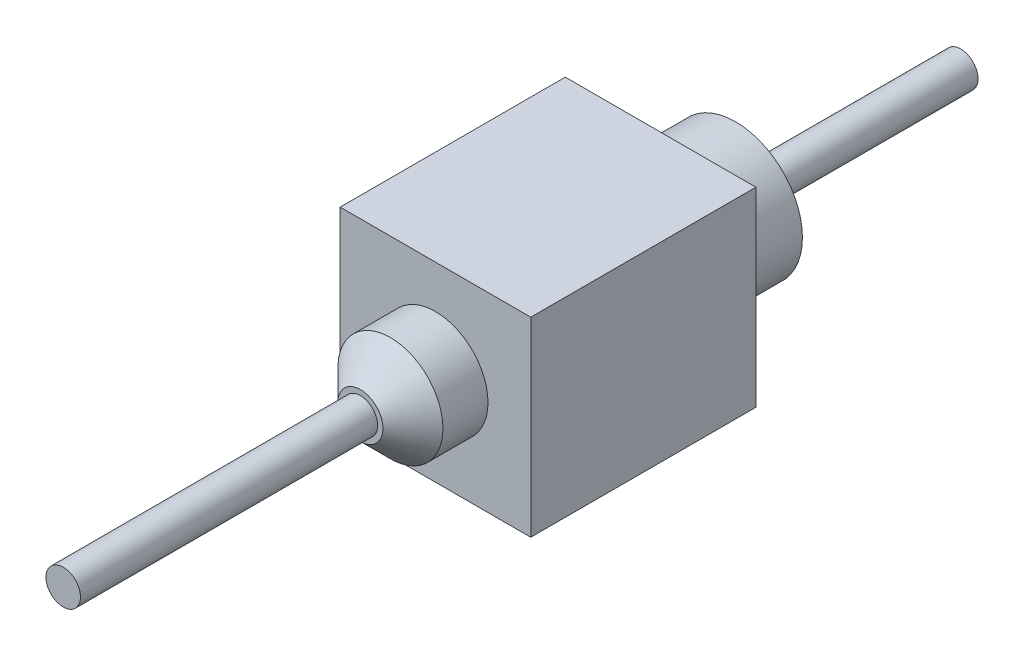
SolidWorks part; units mm, degrees
ref_plane "Front Plane" through (0, 0, 0) normal (0, 0, 1) x (1, 0, 0)
ref_plane "Top Plane" through (0, 0, 0) normal (0, 1, 0) x (1, 0, 0)
ref_plane "Right Plane" through (0, 0, 0) normal (1, 0, 0) x (0, 0, -1)
sketch "Sketch1" plane through (0, 0, 0) normal (0, 0, 1) x (1, 0, 0)
  line L1 (1.27, -1.27) -> (-1.27, -1.27)
  line L2 (1.27, -1.27) -> (1.27, 1.27)
  line L3 (1.27, 1.27) -> (-1.27, 1.27)
  line L4 (-1.27, -1.27) -> (-1.27, 1.27)
  line L5 (1.27, -1.27) -> (-1.27, 1.27) construction
  line L6 (1.27, 1.27) -> (-1.27, -1.27) construction
  point P0 (0, 0)
  dimension "D1" = 2.54
extrude "Boss-Extrude1" add sketch "Sketch1" along normal blind 3
sketch "Sketch2" plane through (0, 0, 0) normal (0, 0, -1) x (-1, 0, 0)
  circle A0 centre (0, 0) radius 0.23
  dimension "D1" = 0.46
extrude "Boss-Extrude2" add sketch "Sketch2" along normal blind 4
sketch "Sketch3" plane through (0, 0, 0) normal (0, 0, -1) x (-1, 0, 0)
  circle A0 centre (0, 0) radius 0.89
  dimension "D1" = 1.78
extrude "Boss-Extrude3" add sketch "Sketch3" along normal blind 1
sketch "Sketch4" plane through (0, 0, 3) normal (0, 0, 1) x (1, 0, 0)
  circle A0 centre (0, 0) radius 0.23
  dimension "D1" = 0.46
extrude "Boss-Extrude4" add sketch "Sketch4" along normal blind 4.96
sketch "Sketch5" plane through (0, 0, 3) normal (0, 0, 1) x (1, 0, 0)
  circle A0 centre (0, 0) radius 0.7
  dimension "D1" = 1.4
extrude "Boss-Extrude5" add sketch "Sketch5" along normal blind 1
chamfer "Chamfer1" distance 0.4 angle 45 1 edges at (0.7, 0, 4)
